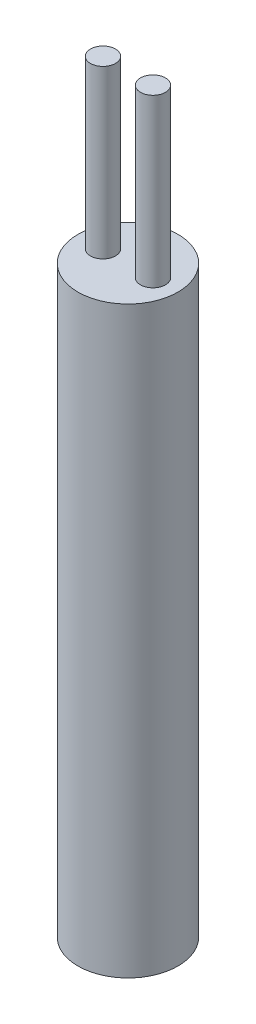
SolidWorks part; units mm, degrees
ref_plane "Front Plane" through (0, 0, 0) normal (0, 0, 1) x (1, 0, 0)
ref_plane "Top Plane" through (0, 0, 0) normal (0, 1, 0) x (1, 0, 0)
ref_plane "Right Plane" through (0, 0, 0) normal (1, 0, 0) x (0, 0, -1)
sketch "Sketch1" plane through (0, 0, 0) normal (0, 1, 0) x (1, 0, 0)
  circle A0 centre (0, 0) radius 3
  dimension "D1" = 6
extrude "Boss-Extrude1" add sketch "Sketch1" along normal blind 35
sketch "Sketch2" plane through (0, 35, 0) normal (0, 1, 0) x (1, 0, 0)
  line L0 (0, -3) -> (0, 3) construction
  circle A0 centre (1.5, 0) radius 0.75
  circle A1 centre (0, 0) radius 3 construction
  circle A2 centre (-1.5, 0) radius 0.75
  dimension "D1" = 1.5
  dimension "D2" = 3
extrude "Boss-Extrude2" add sketch "Sketch2" along normal blind 10
